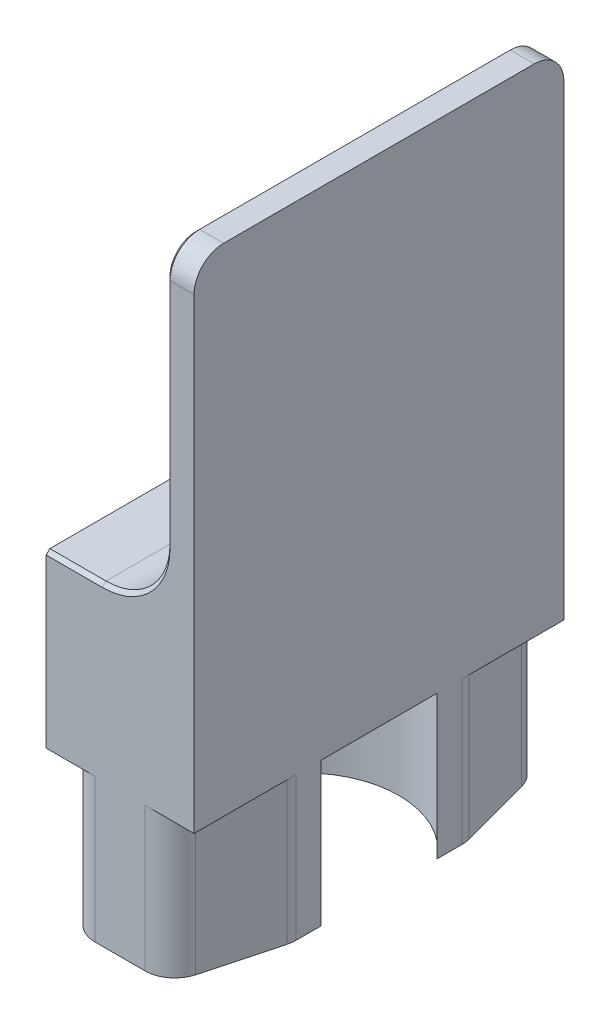
SolidWorks part; units mm, degrees
material "6061-T6 (SS)"
ref_plane "Front Plane" through (0, 0, 0) normal (0, 0, 1) x (1, 0, 0)
ref_plane "Top Plane" through (0, 0, 0) normal (0, 1, 0) x (1, 0, 0)
ref_plane "Right Plane" through (0, 0, 0) normal (1, 0, 0) x (0, 0, -1)
sketch "Sketch2" plane through (0, 0, 0) normal (0, 0, 1) x (1, 0, 0)
  line L0 (3.125, 22.23) -> (3.125, 39.905)
  line L1 (5, 39.905) -> (5, -3.35)
  line L2 (5, -3.35) -> (-5, -3.35)
  line L3 (-1.2, 17.905) -> (-5, 17.905)
  line L4 (-1.2, 17.905) -> (5, 17.905) construction
  line L5 (3.125, 39.905) -> (5, 39.905)
  line L9 (-5, 17.905) -> (-5, -3.35)
  line L10 (0, 0) -> (0, -3.35) construction
  arc A0 (3.125, 22.23) -> (-1.2, 17.905) centre (-1.2, 22.23) cw
  circle A1 centre (0, 0) radius 6.35 construction
  point P4 (0, -6.35)
  point P9 (0, 6.35)
  dimension "D4" = 4.325
  dimension "D3" = 12.7
  dimension "D1" = 22
  dimension "D2" = 22.23
  dimension "D5" = 1.875
  dimension "D6" = 10
  dimension "D7" = 3
  dimension "D9" = 1.2
extrude "Boss-Extrude1" add sketch "Sketch2" along normal mid plane 25
sketch "Sketch3" plane through (0, -3.35, 0) normal (0, -1, 0) x (1, 0, 0)
  circle A2 centre (0, 0) radius 6.3525
  dimension "D1" = 12.705
extrude "Cut-Extrude1" cut sketch "Sketch3" against normal up to vertex (9.7 mm away) up to point (0, 6.35, 0)
fillet "Fillet1" radius 2 2 edges at (4.0625, 39.905, -12.5) (4.0625, 39.905, 12.5)
sketch "Sketch6" plane through (0, -3.35, 0) normal (0, -1, 0) x (1, 0, 0)
  line L0 (0, 24.5442) -> (-5.4215, 4.3108)
  line L1 (0, 24.5442) -> (5.4215, 4.3108)
  line L2 (0, 24.5442) -> (0, 0) construction
  line L3 (-5.4215, 4.3108) -> (-5.4215, 3.3108)
  line L4 (-5.4215, 4.3108) -> (-6.136, 1.6441) construction
  line L5 (5.4215, 4.3108) -> (5.4215, 3.3108)
  line L6 (5.4215, 4.3108) -> (6.136, 1.6441) construction
  line L7 (-5.4215, 3.3108) -> (-5.4215, 0)
  line L8 (-5.4215, 0) -> (-10.4215, 0)
  line L9 (-10.4215, 0) -> (-10.4215, 29.5442)
  line L10 (-10.4215, 29.5442) -> (10.4215, 29.5442)
  line L11 (10.4215, 29.5442) -> (10.4215, 0)
  line L12 (10.4215, 0) -> (5.4215, 0)
  line L13 (5.4215, 0) -> (5.4215, 3.3108)
  circle A0 centre (0, 0) radius 6.3525 construction
  arc A1 (5, 3.9185) -> (-5, 3.9185) centre (0, 0) ccw construction
  dimension "D1" = 15
  dimension "D2" = 1
  dimension "D3" = 5
  dimension "D4" = 5
extrude "Cut-Extrude2" cut sketch "Sketch6" against normal up to surface (9.7 mm away) up to face at (0, 6.35, 0)
mirror "Mirror1" about plane through (0, 0, 0) normal (0, 0, 1) of "Cut-Extrude2"
fillet "Fillet2" radius 2 8 edges at (-5, 1.5, 5.8839) (-3.2272, 1.5, 12.5) (3.2272, 1.5, 12.5) (5, 1.5, 5.8839) (5, 1.5, -5.8839) (3.2272, 1.5, -12.5) (-3.2272, 1.5, -12.5) (-5, 1.5, -5.8839)
sketch "Sketch7" plane through (-5, 0, 0) normal (-1, 0, 0) x (0, 0, 1)
  line L0 (0, 17.905) -> (0, 15.905) construction
  line L1 (-10.5, 15.905) -> (10.5, 15.905)
  line L2 (-10.5, 15.905) -> (-10.5, 8.35)
  line L3 (-10.5, 8.35) -> (10.5, 8.35)
  line L4 (10.5, 15.905) -> (10.5, 8.35)
  line L5 (12.5, 17.905) -> (-12.5, 17.905) construction
  line L6 (-10.5, 12.1275) -> (-12.5, 12.1275) construction
  line L7 (0, 8.35) -> (0, 6.35) construction
  line L8 (3.9185, 6.35) -> (-3.9185, 6.35) construction
  line L10 (-12.5, 17.905) -> (-12.5, 6.35) construction
  dimension "D1" = 2
extrude "Cut-Extrude3" cut sketch "Sketch7" against normal offset from surface (8 mm away) 2 up to face at (5, 12.9392, 0)
fillet "Fillet3" radius 2 4 edges at (-1, 8.35, 10.5) (-1, 8.35, -10.5) (-1, 15.905, 10.5) (-1, 15.905, -10.5)
chamfer "Chamfer1" distance 0.25 angle 45 17 edges at (-3.1, 17.905, -12.5) (1.8582, 19.1718, -12.5) (3.125, 30.0675, -12.5) (3.125, 39.3192, -11.9142) (3.125, 39.905, 0) (-3.1, 17.905, 12.5) (3.125, 39.3192, 11.9142) (1.8582, 19.1718, 12.5) (3.125, 30.0675, 12.5) (-5, 8.35, 0) (-5, 8.9358, 9.9142) (-5, 8.9358, -9.9142) (-5, 12.1275, 10.5) (-5, 12.1275, -10.5) (-5, 15.3192, 9.9142) (-5, 15.3192, -9.9142) (-5, 15.905, 0)
equation "\"ball_diameter\"= 5/32*25.4"
